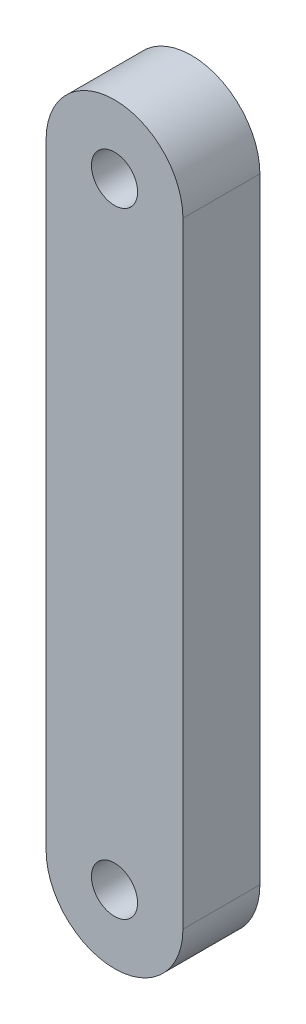
SolidWorks part; units mm, degrees
material "铸造合金钢"
ref_plane "前视基准面" through (0, 0, 0) normal (0, 0, 1) x (1, 0, 0)
ref_plane "上视基准面" through (0, 0, 0) normal (0, 1, 0) x (1, 0, 0)
ref_plane "右视基准面" through (0, 0, 0) normal (1, 0, 0) x (0, 0, -1)
sketch "草图1" plane through (0, 0, 0) normal (0, 0, 1) x (1, 0, 0)
  line L1 (-0.8889, 4) -> (0.8889, 4)
  line L2 (-0.8889, 4) -> (-0.8889, -4)
  line L3 (-0.8889, -4) -> (0.8889, -4)
  line L4 (0.8889, 4) -> (0.8889, -4)
  line L5 (-0.8889, 4) -> (0.8889, -4) construction
  line L6 (-0.8889, -4) -> (0.8889, 4) construction
  circle A0 centre (0, 4) radius 0.8889
  circle A1 centre (0, -4) radius 0.8889
  circle A2 centre (0, 4) radius 0.3
  circle A3 centre (0, -4) radius 0.3
  point P0 (0, 0)
extrude "凸台-拉伸3" add sketch "草图1" along normal blind 1 contours A2 L1 A0 | A2 L1 A0 | A1 L4 A0 L2 | A3 L3 A1 | A3 L3 A1
